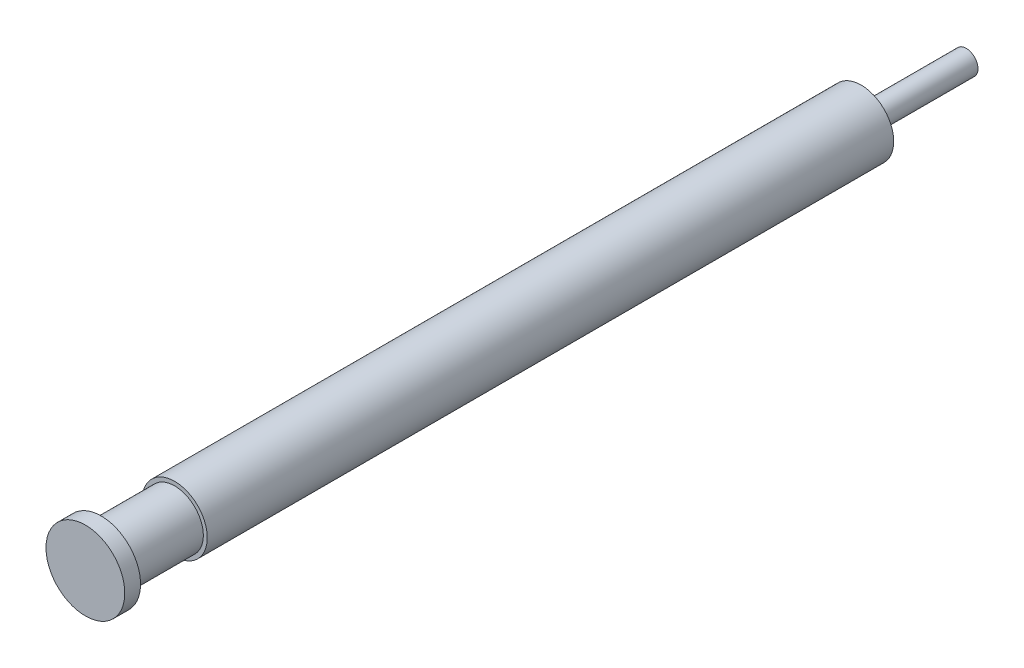
SolidWorks part; units mm, degrees
ref_plane "Front Plane" through (0, 0, 0) normal (0, 0, 1) x (1, 0, 0)
ref_plane "Top Plane" through (0, 0, 0) normal (0, 1, 0) x (1, 0, 0)
ref_plane "Right Plane" through (0, 0, 0) normal (1, 0, 0) x (0, 0, -1)
sketch "linear trace" plane through (0, 0, 0) normal (0, 1, 0) x (1, 0, 0)
  line L0 (160, 640) -> (800, 640) construction
  line L1 (24.8682, 43.7808) -> (24.8682, 17.0056)
  line L2 (24.8682, 17.0056) -> (24.8682, -55.9944)
  line L3 (25.1593, 43.7784) -> (27.244, 18.0728) construction
  line L4 (23.9729, 43.7784) -> (22.4925, 18.0728) construction
  line L5 (22.4925, 18.0728) -> (27.244, 18.0728) construction
  arc A0 (24.9673, 68.7253) -> (22.5853, 64.4044) centre (26.246, 65.2034) ccw
  arc A1 (22.5853, 64.4044) -> (24.8682, 43.7808) centre (-74.4553, 43.2243) cw
  point P13 (24.8682, 18.0728)
sketch "Sketch2" plane through (0, 0, 0) normal (0, 1, 0) x (1, 0, 0)
  line L0 (24.8682, 17.0056) -> (24.8682, -55.9944) construction
  line L1 (24.8682, 43.7808) -> (24.8682, 17.0056) construction
  line L2 (24.8682, 17.0056) -> (24.8682, -55.9944)
  line L3 (24.8682, 43.7808) -> (24.8682, 17.0056) construction
  line L4 (24.8682, 43.7808) -> (25.1344, 43.7808) construction
  line L5 (25.1344, 43.7808) -> (25.9932, 17.8476) construction
  line L6 (27.9682, 17.8476) -> (27.9682, -47.4944)
  line L7 (27.5932, -47.4944) -> (27.5932, -54.4944)
  line L8 (27.5932, -54.4944) -> (28.6182, -54.4944)
  line L9 (28.6182, -54.4944) -> (28.6182, -55.9944)
  line L10 (28.6182, -55.9944) -> (24.8682, -55.9944)
  line L11 (27.5932, -47.4944) -> (27.9682, -47.4944)
  line L12 (25.9932, 17.8476) -> (27.9682, 17.8476)
  line L13 (25.9932, 17.8476) -> (25.9932, 27.8476)
  line L14 (25.9932, 27.8476) -> (24.8682, 27.8476)
  line L15 (24.8682, 27.8476) -> (24.8682, 17.0056)
  dimension "D1" = 3.1
  dimension "D2" = 73
  dimension "D3" = 2.725
  dimension "D4" = 3.75
  dimension "D5" = 1.5
  dimension "D6" = 7
  dimension "D7" = 1.125
  dimension "D8" = 10
revolve "Revolve4" add sketch "Sketch2" angle 360 about L2
ref_plane "Plane1" [suppressed] through (0, 0, 55.9944) normal (0, 0, 1) x (1, 0, 0)
sketch "Sketch3" plane through (0, 0, 55.9944) normal (0, 0, 1) x (1, 0, 0)
  circle A0 centre (24.8682, 0) radius 0.75
  circle A1 centre (24.8682, 0) radius 3.75 construction
  circle A2 centre (24.8682, 0) radius 3.75 construction
  dimension "D1" = 1.5
extrude "Cut-Extrude6" [suppressed] cut sketch "Sketch3" against normal through all contours A0
